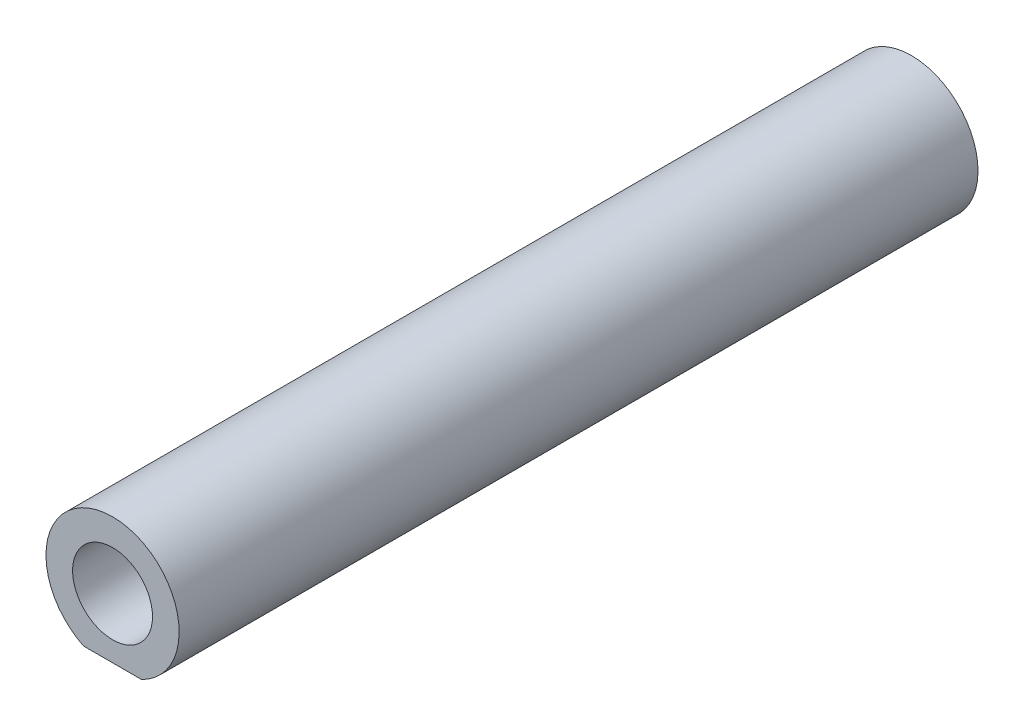
SolidWorks part; units mm, degrees
ref_plane "Front Plane" through (0, 0, 0) normal (0, 0, 1) x (1, 0, 0)
ref_plane "Top Plane" through (0, 0, 0) normal (0, 1, 0) x (1, 0, 0)
ref_plane "Right Plane" through (0, 0, 0) normal (1, 0, 0) x (0, 0, -1)
sketch "Sketch1" plane through (0, 0, 0) normal (0, 0, 1) x (1, 0, 0)
  circle A0 centre (0, 0) radius 5
  circle A1 centre (0, 0) radius 3
  dimension "D1" = 10
  dimension "D2" = 6
extrude "Boss-Extrude1" add sketch "Sketch1" along normal mid plane 60
sketch "Sketch4" plane through (0, 0, 30) normal (0, 0, 1) x (1, 0, 0)
  line L0 (2.1794, -4.5) -> (-2.1794, -4.5)
  circle A0 centre (0, 0) radius 5 construction
  arc A1 (-2.1794, -4.5) -> (2.1794, -4.5) centre (0, 0) ccw
  point P5 (2.1794, -4.5)
  point P6 (-2.1794, -4.5)
  point P7 (6.3929, -4.0613)
  dimension "D1" = 4.5
extrude "Cut-Extrude2" cut sketch "Sketch4" against normal blind 10 contours A1 L0
mirror "Mirror3" about plane through (0, 0, 0) normal (0, 0, 1) of "Cut-Extrude2"
